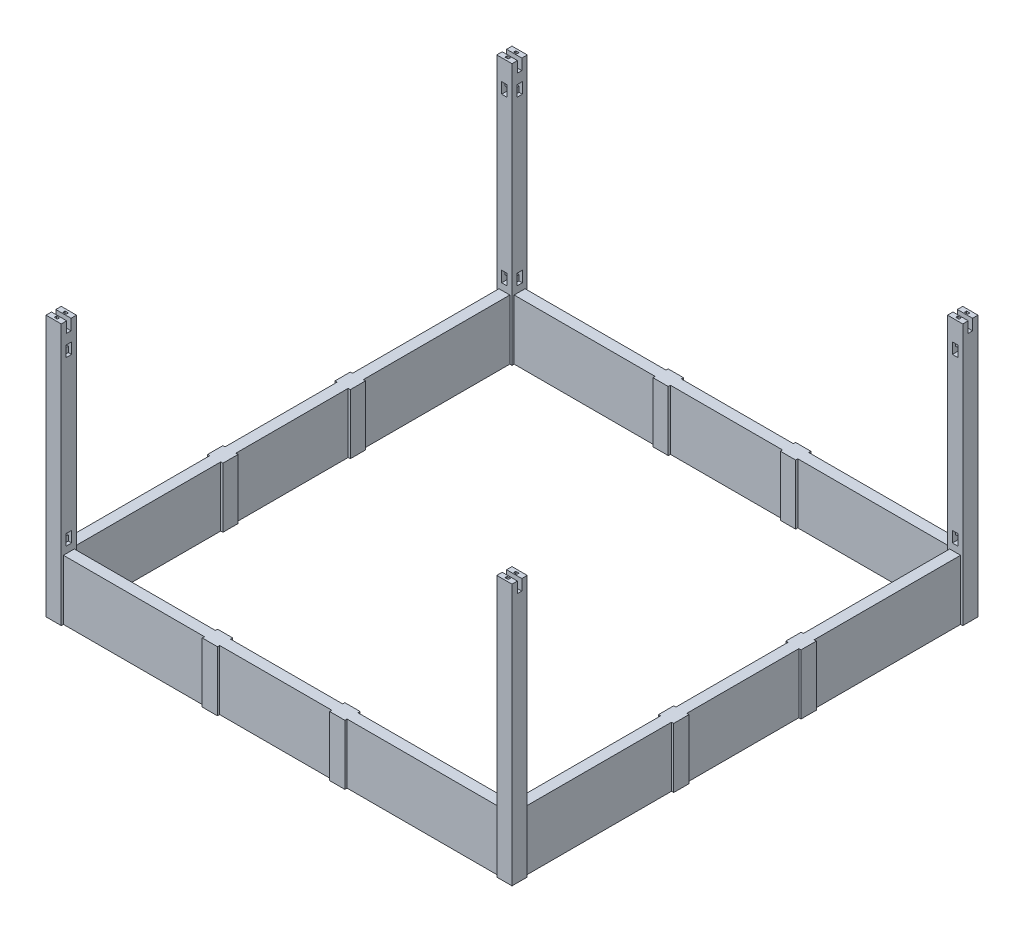
SolidWorks part; units mm, degrees
material "松木"
ref_plane "前视基准面" through (0, 0, 0) normal (0, 0, 1) x (1, 0, 0)
ref_plane "上视基准面" through (0, 0, 0) normal (0, 1, 0) x (1, 0, 0)
ref_plane "右视基准面" through (0, 0, 0) normal (1, 0, 0) x (0, 0, -1)
sketch "草图1" plane through (0, 0, 0) normal (0, 1, 0) x (1, 0, 0)
  line L1 (0, 0) -> (4280, 0)
  line L2 (0, 0) -> (0, 4280)
  line L3 (0, 4280) -> (4280, 4280)
  line L4 (4280, 0) -> (4280, 4280)
  line L5 (0, 4280) -> (140, 4280)
  line L6 (0, 4280) -> (0, 4140)
  line L7 (0, 4140) -> (140, 4140)
  line L8 (140, 4280) -> (140, 4140)
  line L9 (4280, 4280) -> (4140, 4280)
  line L10 (4280, 4280) -> (4280, 4140)
  line L11 (4280, 4140) -> (4140, 4140)
  line L12 (4140, 4280) -> (4140, 4140)
  line L13 (4280, 0) -> (4140, 0)
  line L14 (4280, 0) -> (4280, 140)
  line L15 (4280, 140) -> (4140, 140)
  line L16 (4140, 0) -> (4140, 140)
  line L17 (0, 0) -> (140, 0)
  line L18 (0, 0) -> (0, 140)
  line L19 (0, 140) -> (140, 140)
  line L20 (140, 0) -> (140, 140)
  dimension "D1" = 4280
  dimension "D2" = 4280
  dimension "D3" = 140
  dimension "D4" = 140
extrude "凸台-拉伸1" add sketch "草图1" along normal blind 2400 contours L8 L3 L2 L7 | L3 L12 L11 L4 | L16 L1 L4 L15 | L1 L20 L19 L2
sketch "草图2" plane through (0, 0, 0) normal (0, -1, 0) x (1, 0, 0)
  line L0 (0, -140) -> (140, -140) construction
  line L1 (90, -140) -> (140, -140)
  line L2 (90, -140) -> (90, 0)
  line L3 (90, 0) -> (140, 0)
  line L4 (140, -140) -> (140, 0)
  line L5 (0, 0) -> (140, 0) construction
  line L6 (0, -140) -> (50, -140)
  line L7 (0, -140) -> (0, 0)
  line L8 (0, 0) -> (50, 0)
  line L9 (50, -140) -> (50, 0)
  line L11 (50, 0) -> (90, 0)
  line L12 (50, 0) -> (50, -20)
  line L13 (50, -20) -> (90, -20)
  line L14 (90, 0) -> (90, -20)
  line L15 (90, -140) -> (50, -140)
  line L16 (90, -140) -> (90, -120)
  line L17 (90, -120) -> (50, -120)
  line L18 (50, -140) -> (50, -120)
  dimension "D1" = 50
  dimension "D2" = 50
  dimension "D3" = 20
  dimension "D4" = 20
extrude "切除-拉伸1" cut sketch "草图2" against normal blind 100 contours L17 L2 L13 L9
pattern_linear "阵列(线性)1" count 2 spacing 4140 along (1, 0, 0) count 2 spacing 4140 along (0, 0, -1) of "切除-拉伸1"
sketch "草图3" plane through (140, 0, 0) normal (1, 0, 0) x (0, 0, -1)
  line L5 (0, 0) -> (140, 0) construction
  line L6 (20, 0) -> (120, 0)
  line L7 (20, 0) -> (20, 550)
  line L8 (20, 550) -> (120, 550)
  line L9 (120, 0) -> (120, 550)
  line L10 (0, 2400) -> (140, 2400) construction
  point P7 (70, 0)
  point P10 (70, 2400)
  dimension "D1" = 100
  dimension "D2" = 550
extrude "凸台-拉伸2" add sketch "草图3" along normal blind 4000 contours L6 L9 L8 L7
pattern_linear "阵列(线性)2" count 2 spacing 4140 along (0, 0, -1) of "凸台-拉伸2"
sketch "草图4" plane through (0, 0, -140) normal (0, 0, -1) x (-1, 0, 0)
  line L0 (0, 0) -> (-140, 0) construction
  line L1 (-120, 0) -> (-20, 0)
  line L2 (-120, 0) -> (-120, 550)
  line L3 (-120, 550) -> (-20, 550)
  line L4 (-20, 0) -> (-20, 550)
  line L5 (0, 2400) -> (-140, 2400) construction
  point P6 (-70, 550)
  point P9 (-70, 2400)
  dimension "D1" = 550
  dimension "D2" = 100
extrude "凸台-拉伸3" add sketch "草图4" along normal blind 4000
pattern_linear "阵列(线性)4" count 2 spacing 4140 along (1, 0, 0) of "凸台-拉伸3"
sketch "草图5" plane through (0, 0, 0) normal (0, -1, 0) x (1, 0, 0)
  line L0 (0, 0) -> (0, -140) construction
  line L1 (0, -1485) -> (140, -1485)
  line L2 (0, -1485) -> (0, -1625)
  line L3 (0, -1625) -> (140, -1625)
  line L4 (140, -1485) -> (140, -1625)
  line L5 (90, -120) -> (50, -120) construction
  dimension "D1" = 140
  dimension "D2" = 140
  dimension "D3" = 1365
extrude "凸台-拉伸4" add sketch "草图5" against normal blind 550
sketch "草图6" plane through (0, 0, 0) normal (0, -1, 0) x (1, 0, 0)
  line L0 (0, -1485) -> (0, -1625) construction
  line L1 (90, -1605) -> (50, -1605)
  line L2 (90, -1605) -> (90, -1505)
  line L3 (90, -1505) -> (50, -1505)
  line L4 (50, -1605) -> (50, -1505)
  line L5 (0, -1625) -> (20, -1625) construction
  point P6 (70, -1605)
  dimension "D1" = 100
  dimension "D2" = 40
  dimension "D3" = 50
  dimension "D4" = 20
extrude "切除-拉伸2" cut sketch "草图6" against normal blind 100
pattern_linear "阵列(线性)5" count 2 spacing 1170 along (0, 0, -1) count 2 spacing 4140 along (1, 0, 0) of "切除-拉伸2", "凸台-拉伸4"
sketch "草图8" plane through (0, 0, 0) normal (0, -1, 0) x (1, 0, 0)
  line L0 (0, 0) -> (0, -140) construction
  line L1 (1455, -50) -> (1555, -50)
  line L2 (1455, -50) -> (1455, -90)
  line L3 (1455, -90) -> (1555, -90)
  line L4 (1555, -50) -> (1555, -90)
  line L5 (4140, -20) -> (140, -20) construction
  line L7 (1575, -140) -> (1435, -140)
  line L8 (1575, -140) -> (1575, 0)
  line L9 (1575, 0) -> (1435, 0)
  line L10 (1435, -140) -> (1435, 0)
  point P12 (1505, -140)
  point P13 (1505, -90)
  dimension "D1" = 100
  dimension "D2" = 40
  dimension "D3" = 1455
  dimension "D4" = 30
  dimension "D5" = 140
  dimension "D6" = 140
  dimension "D7" = 50
extrude "凸台-拉伸5" add sketch "草图8" against normal blind 550
sketch "草图10" plane through (0, 0, 0) normal (0, -1, 0) x (1, 0, 0)
  line L4 (1435, -140) -> (1575, -140)
  line L5 (1435, 0) -> (1435, -140)
  line L6 (1575, 0) -> (1435, 0)
  line L7 (1575, -140) -> (1575, 0)
  line L8 (1435, -140) -> (1575, -140)
  line L9 (1435, 0) -> (1435, -140)
  line L10 (1575, 0) -> (1435, 0)
  line L11 (1575, -140) -> (1575, 0)
  line L12 (1555, -50) -> (1455, -50)
  line L13 (1555, -90) -> (1555, -50)
  line L14 (1455, -90) -> (1555, -90)
  line L15 (1455, -50) -> (1455, -90)
  line L16 (1555, -50) -> (1455, -50)
  line L17 (1555, -90) -> (1555, -50)
  line L18 (1455, -90) -> (1555, -90)
  line L19 (1455, -50) -> (1455, -90)
  line L40 (4140, -20) -> (1575, -20)
  line L41 (1575, -20) -> (1575, 0)
  line L42 (1575, 0) -> (1435, 0)
  line L43 (1435, 0) -> (1435, -20)
  line L44 (1435, -20) -> (140, -20)
  line L45 (140, -20) -> (140, 0)
  line L46 (140, 0) -> (0, 0)
  line L47 (0, 0) -> (0, -140)
  line L48 (0, -140) -> (20, -140)
  line L49 (20, -140) -> (20, -1485)
  line L50 (20, -1485) -> (0, -1485)
  line L51 (0, -1485) -> (0, -1625)
  line L52 (0, -1625) -> (20, -1625)
  line L53 (20, -1625) -> (20, -2655)
  line L54 (20, -2655) -> (0, -2655)
  line L55 (0, -2655) -> (0, -2795)
  line L56 (0, -2795) -> (20, -2795)
  line L57 (20, -2795) -> (20, -4140)
  line L58 (20, -4140) -> (0, -4140)
  line L59 (0, -4140) -> (0, -4280)
  line L60 (0, -4280) -> (140, -4280)
  line L61 (140, -4280) -> (140, -4260)
  line L62 (140, -4260) -> (4140, -4260)
  line L63 (4140, -4260) -> (4140, -4280)
  line L64 (4140, -4280) -> (4280, -4280)
  line L65 (4280, -4280) -> (4280, -4140)
  line L66 (4280, -4140) -> (4260, -4140)
  line L67 (4260, -4140) -> (4260, -2795)
  line L68 (4260, -2795) -> (4280, -2795)
  line L69 (4280, -2795) -> (4280, -2655)
  line L70 (4280, -2655) -> (4260, -2655)
  line L71 (4260, -2655) -> (4260, -1625)
  line L72 (4260, -1625) -> (4280, -1625)
  line L73 (4280, -1625) -> (4280, -1485)
  line L74 (4280, -1485) -> (4260, -1485)
  line L75 (4260, -1485) -> (4260, -140)
  line L76 (4260, -140) -> (4280, -140)
  line L77 (4280, -140) -> (4280, 0)
  line L78 (4280, 0) -> (4140, 0)
  line L79 (4140, 0) -> (4140, -20)
  line L80 (4140, -20) -> (1575, -20)
  line L81 (1575, -20) -> (1575, 0)
  line L82 (1575, 0) -> (1435, 0)
  line L83 (1435, 0) -> (1435, -20)
  line L84 (1435, -20) -> (140, -20)
  line L85 (140, -20) -> (140, 0)
  line L86 (140, 0) -> (0, 0)
  line L87 (0, 0) -> (0, -140)
  line L88 (0, -140) -> (20, -140)
  line L89 (20, -140) -> (20, -1485)
  line L90 (20, -1485) -> (0, -1485)
  line L91 (0, -1485) -> (0, -1625)
  line L92 (0, -1625) -> (20, -1625)
  line L93 (20, -1625) -> (20, -2655)
  line L94 (20, -2655) -> (0, -2655)
  line L95 (0, -2655) -> (0, -2795)
  line L96 (0, -2795) -> (20, -2795)
  line L97 (20, -2795) -> (20, -4140)
  line L98 (20, -4140) -> (0, -4140)
  line L99 (0, -4140) -> (0, -4280)
  line L100 (0, -4280) -> (140, -4280)
  line L101 (140, -4280) -> (140, -4260)
  line L102 (140, -4260) -> (4140, -4260)
  line L103 (4140, -4260) -> (4140, -4280)
  line L104 (4140, -4280) -> (4280, -4280)
  line L105 (4280, -4280) -> (4280, -4140)
  line L106 (4280, -4140) -> (4260, -4140)
  line L107 (4260, -4140) -> (4260, -2795)
  line L108 (4260, -2795) -> (4280, -2795)
  line L109 (4280, -2795) -> (4280, -2655)
  line L110 (4280, -2655) -> (4260, -2655)
  line L111 (4260, -2655) -> (4260, -1625)
  line L112 (4260, -1625) -> (4280, -1625)
  line L113 (4280, -1625) -> (4280, -1485)
  line L114 (4280, -1485) -> (4260, -1485)
  line L115 (4260, -1485) -> (4260, -140)
  line L116 (4260, -140) -> (4280, -140)
  line L117 (4280, -140) -> (4280, 0)
  line L118 (4280, 0) -> (4140, 0)
  line L119 (4140, 0) -> (4140, -20)
  dimension "D1" = 0
  dimension "D2" = 0
  dimension "D3" = 0
extrude "切除-拉伸3" cut sketch "草图10" against normal blind 100 contours L16 L19 L18 L17
pattern_linear "阵列(线性)6" count 2 spacing 1170 along (1, 0, 0) count 2 spacing 4140 along (0, 0, -1) of "切除-拉伸3", "凸台-拉伸5"
sketch "草图11" plane through (0, 2400, 0) normal (0, 1, 0) x (1, 0, 0)
  line L0 (0, 0) -> (0, 140) construction
  line L1 (0, 50) -> (140, 50)
  line L2 (0, 50) -> (0, 90)
  line L3 (0, 90) -> (140, 90)
  line L4 (140, 50) -> (140, 90)
  line L5 (140, 0) -> (140, 140) construction
  line L6 (0, 0) -> (140, 0) construction
  dimension "D1" = 40
  dimension "D2" = 50
extrude "切除-拉伸4" cut sketch "草图11" against normal blind 100
pattern_linear "阵列(线性)7" count 2 spacing 4140 along (1, 0, 0) count 2 spacing 4140 along (0, 0, -1) of "切除-拉伸4"
sketch "草图12" plane through (0, 2400, 0) normal (0, 1, 0) x (1, 0, 0)
  line L0 (4280, 140) -> (4140, 140) construction
  line L1 (4225, 120) -> (4195, 120)
  line L2 (4225, 120) -> (4225, 100)
  line L3 (4225, 100) -> (4195, 100)
  line L4 (4195, 120) -> (4195, 100)
  line L5 (4225, 40) -> (4195, 40)
  line L6 (4225, 40) -> (4225, 20)
  line L7 (4225, 20) -> (4195, 20)
  line L8 (4195, 40) -> (4195, 20)
  line L9 (4140, 0) -> (4280, 0) construction
  line L10 (4140, 0) -> (4140, 50) construction
  point P10 (4210, 120)
  point P13 (4210, 0)
  dimension "D1" = 30
  dimension "D2" = 20
  dimension "D3" = 20
  dimension "D4" = 20
  dimension "D5" = 55
extrude "切除-拉伸5" cut sketch "草图12" against normal blind 50
pattern_linear "阵列(线性)8" count 2 spacing 4140 along (0, 0, -1) count 2 spacing 4140 along (-1, 0, 0) of "切除-拉伸5"
sketch "草图13" plane through (140, 0, 0) normal (1, 0, 0) x (0, 0, -1)
  line L0 (20, 550) -> (120, 550) construction
  line L1 (45, 610) -> (95, 610)
  line L2 (45, 610) -> (45, 710)
  line L3 (45, 710) -> (95, 710)
  line L4 (95, 610) -> (95, 710)
  point P6 (70, 610)
  point P7 (70, 550)
  dimension "D1" = 60
  dimension "D2" = 50
  dimension "D3" = 100
extrude "切除-拉伸6" cut sketch "草图13" against normal blind 30
sketch "草图14" plane through (110, 0, 0) normal (1, 0, 0) x (0, 0, -1)
  line L0 (95, 610) -> (95, 710) construction
  line L1 (45, 710) -> (95, 710)
  line L2 (45, 710) -> (45, 660)
  line L3 (45, 660) -> (95, 660)
  line L4 (95, 710) -> (95, 660)
extrude "切除-拉伸7" cut sketch "草图14" against normal blind 50
pattern_linear "阵列(线性)9" count 2 spacing 1500 along (0, 1, 0) of "切除-拉伸7", "切除-拉伸6"
ref_plane "基准面1" through (2140, 0, 0) normal (1, 0, 0) x (0, 0, -1)
mirror "镜向1" about plane through (2140, 0, 0) normal (1, 0, 0) of "切除-拉伸6", "切除-拉伸7", "阵列(线性)9"
ref_plane "基准面2" through (0, 0, -2140) normal (0, 0, 1) x (1, 0, 0)
mirror "镜向2" about plane through (0, 0, -2140) normal (0, 0, 1) of "镜向1", "切除-拉伸6", "切除-拉伸7", "阵列(线性)9"
sketch "草图15" plane through (0, 0, -140) normal (0, 0, -1) x (-1, 0, 0)
  line L0 (-20, 550) -> (-120, 550) construction
  line L1 (-95, 610) -> (-45, 610)
  line L2 (-95, 610) -> (-95, 710)
  line L3 (-95, 710) -> (-45, 710)
  line L4 (-45, 610) -> (-45, 710)
  point P6 (-70, 610)
  point P7 (-70, 550)
  dimension "D1" = 60
  dimension "D2" = 50
  dimension "D3" = 100
extrude "切除-拉伸8" cut sketch "草图15" against normal blind 30
sketch "草图16" plane through (0, 0, -110) normal (0, 0, -1) x (-1, 0, 0)
  line L0 (-45, 610) -> (-45, 710) construction
  line L1 (-95, 610) -> (-45, 610)
  line L2 (-95, 610) -> (-95, 660)
  line L3 (-95, 660) -> (-45, 660)
  line L4 (-45, 610) -> (-45, 660)
  dimension "D1" = 50
extrude "切除-拉伸9" cut sketch "草图16" against normal blind 50
pattern_linear "阵列(线性)10" count 2 spacing 1500 along (0, 1, 0) of "切除-拉伸9", "切除-拉伸8"
mirror "镜向3" about plane through (0, 0, -2140) normal (0, 0, 1) of "阵列(线性)10", "切除-拉伸8", "切除-拉伸9"
mirror "镜向4" about plane through (2140, 0, 0) normal (1, 0, 0) of "镜向3", "切除-拉伸8", "切除-拉伸9", "阵列(线性)10"
